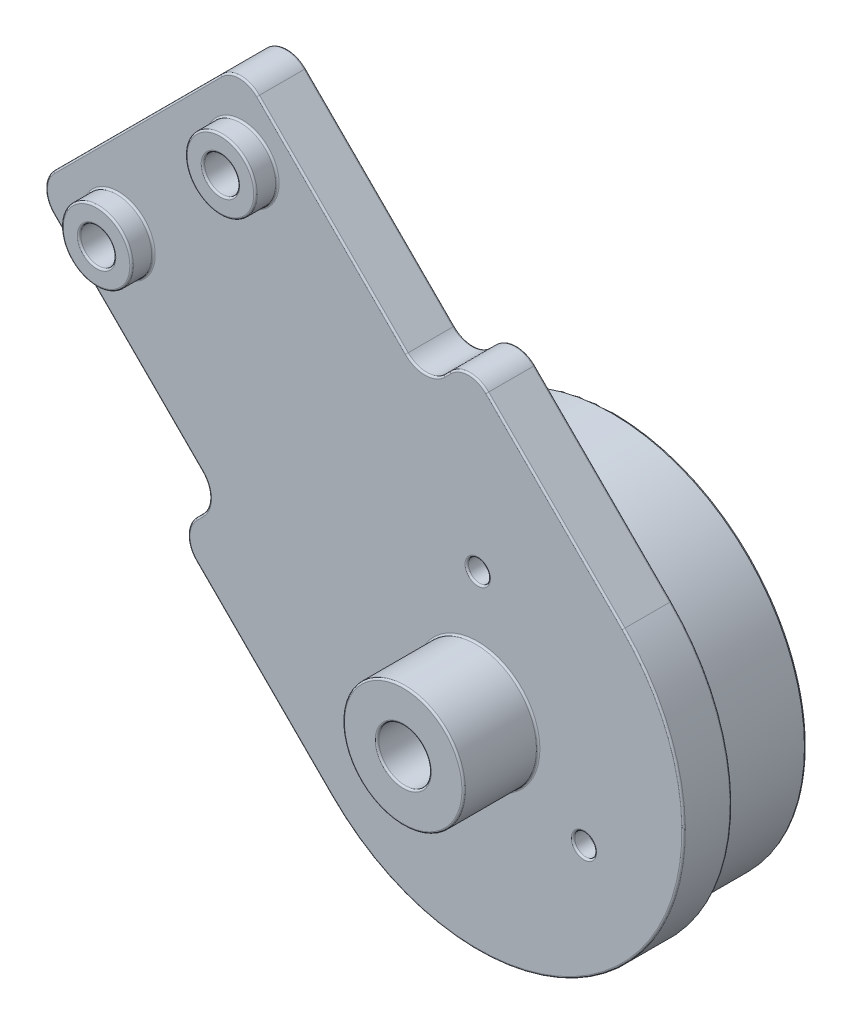
SolidWorks part; units mm, degrees
ref_plane "Front Plane" through (0, 0, 0) normal (0, 0, 1) x (1, 0, 0)
ref_plane "Top Plane" through (0, 0, 0) normal (0, 1, 0) x (1, 0, 0)
ref_plane "Right Plane" through (0, 0, 0) normal (1, 0, 0) x (0, 0, -1)
sketch "Sketch1" plane through (0, 0, 0) normal (0, 0, 1) x (1, 0, 0)
  line L0 (-100, 0) -> (100, 0) construction
  line L1 (-100, 0) -> (0, 100) construction
  line L2 (0, 100) -> (100, 0) construction
  line L3 (0, 0) -> (-50, 50) construction
  line L4 (-40, 60) -> (40, 60) construction
  line L5 (0, 100) -> (0, 60) construction
  circle A0 centre (-100, 0) radius 20
  circle A1 centre (0, 0) radius 20
  circle A2 centre (100, 0) radius 20
  point P2 (0, 0)
  dimension "D5" = 40
  dimension "D1" = 200
  dimension "D2" = 90
  dimension "D3" = 90
  dimension "D4" = 80
sketch "Sketch2" plane through (0, 0, 0) normal (0, 0, 1) x (1, 0, 0)
  line L0 (93.636, 20.5061) -> (79.4939, 6.364)
  line L1 (90.9809, 17.8509) -> (104.534, 4.6576)
  line L2 (-57.0711, 42.9289) -> (-40, 60) construction
  line L3 (-100, 0) -> (0, 100) construction
  line L4 (-40, 60) -> (40, 60) construction
  line L5 (40, 60) -> (86.565, 13.435) construction
  line L6 (0, 100) -> (100, 0) construction
  line L7 (-50, 35.8579) -> (-35.8579, 50)
  line L8 (-35.8579, 50) -> (35.8579, 50)
  line L9 (35.8579, 50) -> (79.4939, 6.364)
  line L10 (-64.1421, 50) -> (-44.1421, 70)
  line L11 (-44.1421, 70) -> (44.1421, 70)
  line L12 (44.1421, 70) -> (93.636, 20.5061)
  line L13 (-64.1421, 50) -> (-50, 35.8579)
  line L14 (82.1491, 9.0191) -> (95.3424, -4.534)
  line L15 (90.1005, 24.0416) -> (75.9584, 9.8995) construction
  line L17 (0, 100) -> (0, 60) construction
  line L18 (6, 70) -> (3.4304, 82.6944)
  line L19 (-6, 70) -> (-3.4304, 82.6944)
  circle A0 centre (100, 0) radius 3.5
  circle A1 centre (100, 0) radius 10 construction
  arc A2 (95.3424, -4.534) -> (104.534, 4.6576) centre (100, 0) ccw
  circle A3 centre (100, 0) radius 20 construction
  circle A4 centre (100, 0) radius 6.5 construction
  circle A5 centre (86.565, 20.5061) radius 1
  circle A6 centre (79.4939, 13.435) radius 1
  circle A7 centre (0, 60) radius 1.5
  circle A9 centre (0, 82) radius 1.5
  arc A10 (3.4304, 82.6944) -> (-3.4304, 82.6944) centre (0, 82) ccw
  circle A11 centre (0, 82) radius 3.5 construction
  circle A13 centre (-50, 50) radius 1.5
  dimension "D4" = 20
  dimension "D5" = 7
  dimension "D9" = 2
  dimension "D12" = 3
  dimension "D18" = 3
  dimension "D3" = 20
  dimension "D7" = 19
  dimension "D8" = 5
  dimension "D10" = 5
  dimension "D11" = 5
  dimension "D13" = 12
  dimension "D15" = 6
  dimension "D16" = 6
  dimension "D1" = 10
  dimension "D2" = 10
  dimension "D6" = 3
  dimension "D14" = 2
sketch "Sketch3" plane through (0, 0, 0) normal (0, 0, 1) x (1, 0, 0)
  line L0 (-86.565, 13.435) -> (-50, 50) construction
  line L1 (-100, 0) -> (0, 100) construction
  line L2 (-50, 50) -> (-13.435, 13.435) construction
  line L3 (0, 0) -> (-50, 50) construction
  line L4 (-79.4939, 6.364) -> (-50, 35.8579)
  line L5 (-50, 35.8579) -> (-20.5061, 6.364)
  line L6 (-93.636, 20.5061) -> (-50, 64.1421)
  line L7 (-50, 64.1421) -> (-6.364, 20.5061)
  line L8 (-79.4939, 6.364) -> (-50, 35.8579) construction
  line L9 (-93.636, 20.5061) -> (-50, 64.1421) construction
  line L10 (-93.636, 20.5061) -> (-79.4939, 6.364)
  line L11 (-6.364, 20.5061) -> (-20.5061, 6.364)
  line L12 (-104.534, 4.6576) -> (-90.9809, 17.8509)
  line L13 (-95.4038, -4.5962) -> (-81.9688, 8.8388)
  line L14 (4.5962, 4.5962) -> (-8.8388, 18.0312)
  line L15 (-4.5962, -4.5962) -> (-18.0312, 8.8388)
  line L16 (-90.1005, 24.0416) -> (-75.9584, 9.8995) construction
  line L17 (-9.8995, 24.0416) -> (-24.0416, 9.8995) construction
  circle A0 centre (-100, 0) radius 3.5
  circle A1 centre (0, 0) radius 3.5
  circle A2 centre (-100, 0) radius 10 construction
  circle A3 centre (0, 0) radius 10 construction
  arc A4 (-104.534, 4.6576) -> (-95.4038, -4.5962) centre (-100, 0) ccw
  arc A5 (-4.5962, -4.5962) -> (4.5962, 4.5962) centre (0, 0) ccw
  circle A6 centre (-100, 0) radius 20 construction
  circle A7 centre (-100, 0) radius 6.5 construction
  circle A8 centre (0, 0) radius 6.5 construction
  circle A9 centre (-86.565, 20.5061) radius 1
  circle A10 centre (-79.4939, 13.435) radius 1
  circle A11 centre (-20.5061, 13.435) radius 1
  circle A12 centre (-13.435, 20.5061) radius 1
  circle A13 centre (-50, 50) radius 1.5 construction
  circle A14 centre (-50, 50) radius 1.5
  dimension "D1" = 7
  dimension "D2" = 20
  dimension "D3" = 3
  dimension "D8" = 2
  dimension "D6" = 19
  dimension "D7" = 19
  dimension "D9" = 5
  dimension "D10" = 5
  dimension "D11" = 5
  dimension "D12" = 5
  dimension "D13" = 5
  dimension "D14" = 5
  dimension "D4" = 10
  dimension "D5" = 10
sketch "Sketch5" plane through (0, 0, 0) normal (0, 0, 1) x (1, 0, 0)
  line L6 (4, 60) -> (4, 70)
  line L7 (-4, 60) -> (-4, 70)
  line L10 (-57.5, 93.3579) -> (57.5, 93.3579)
  line L11 (57.5, 93.3579) -> (57.5, 83.3579)
  line L12 (57.5, 83.3579) -> (44.1421, 70)
  line L13 (44.1421, 70) -> (-44.1421, 70)
  line L14 (-44.1421, 70) -> (-57.5, 83.3579)
  line L15 (-57.5, 83.3579) -> (-57.5, 93.3579)
  line L16 (-22.5, 84.8579) -> (22.5, 84.8579) construction
  line L17 (-22.5, 89.3579) -> (22.5, 89.3579)
  line L18 (-22.5, 80.3579) -> (22.5, 80.3579)
  circle A0 centre (0, 60) radius 1.5 construction
  circle A1 centre (0, 60) radius 1.5
  arc A2 (-4, 60) -> (4, 60) centre (0, 60) ccw
  circle A3 centre (0, 60) radius 4 construction
  arc A4 (-22.5, 89.3579) -> (-22.5, 80.3579) centre (-22.5, 84.8579) ccw
  arc A5 (22.5, 80.3579) -> (22.5, 89.3579) centre (22.5, 84.8579) ccw
  point P2 (0, 93.3579)
  point P7 (0, 84.8579)
  dimension "D1" = 115
  dimension "D2" = 10
  dimension "D3" = 2.5
  dimension "D4" = 45
  dimension "D5" = 9
  dimension "D6" = 4
sketch "Sketch6" plane through (0, 0, 0) normal (0, 0, 1) x (1, 0, 0)
  line L0 (86.3882, 25.2791) -> (74.7209, 13.6118)
  line L1 (0, 100) -> (100, 0) construction
  line L2 (90.1005, 24.0416) -> (75.9584, 9.8995) construction
  line L3 (74.7209, 13.6118) -> (85.3275, 3.0052)
  line L4 (85.3275, 3.0052) -> (82.8527, 0.5303)
  line L5 (82.8527, 0.5303) -> (91.6915, -8.3085)
  line L6 (100, 0) -> (88.4373, 11.5627) construction
  line L7 (99.4697, 17.1473) -> (108.3085, 8.3085)
  line L8 (96.9948, 14.6725) -> (99.4697, 17.1473)
  line L9 (86.3882, 25.2791) -> (96.9948, 14.6725)
  circle A0 centre (100, 0) radius 10 construction
  circle A1 centre (100, 0) radius 10
  arc A2 (91.6915, -8.3085) -> (108.3085, 8.3085) centre (100, 0) ccw
  circle A3 centre (100, 0) radius 11.75 construction
  circle A4 centre (86.565, 20.5061) radius 1 construction
  circle A5 centre (79.4939, 13.435) radius 1 construction
  circle A6 centre (86.565, 20.5061) radius 1
  circle A7 centre (79.4939, 13.435) radius 1
  point P9 (80.5546, 19.4454)
  dimension "D2" = 16.5
  dimension "D3" = 12.5
  dimension "D4" = 15
  dimension "D1" = 1.75
extrude "Boss-Extrude1" add sketch "Sketch6" along normal blind 2.75
sketch "Sketch7" plane through (0, 0, 2.75) normal (0, 0, 1) x (1, 0, 0)
  circle A0 centre (100, 0) radius 10 construction
  circle A1 centre (100, 0) radius 10
extrude "Boss-Extrude2" add sketch "Sketch7" against normal blind 1
sketch "Sketch9" plane through (0, 0, 0) normal (0, 0, -1) x (-1, 0, 0)
  circle A0 centre (-100, 0) radius 11
  circle A1 centre (-100, 0) radius 10
  circle A2 centre (-100, 0) radius 10
  dimension "D1" = 0
  dimension "D2" = 1
extrude "Boss-Extrude3" add sketch "Sketch9" along normal blind 5
fillet "Fillet1" radius 1.5 6 edges at (96.9948, 14.6725, 1.375) (99.4697, 17.1473, 1.375) (82.8527, 0.5303, 1.375) (85.3275, 3.0052, 1.375) (74.7209, 13.6118, 1.375) (86.3882, 25.2791, 1.375)
sketch "Sketch10" plane through (0, 0, 2.75) normal (0, 0, 1) x (1, 0, 0)
  circle A0 centre (79.4939, 13.435) radius 1 construction
  circle A1 centre (86.565, 20.5061) radius 1 construction
  circle A2 centre (79.4939, 13.435) radius 1
  circle A3 centre (86.565, 20.5061) radius 1
  circle A4 centre (79.4939, 13.435) radius 2
  circle A5 centre (86.565, 20.5061) radius 2
  dimension "D1" = 1
extrude "Boss-Extrude4" add sketch "Sketch10" along normal blind 1.25
sketch "Sketch11" plane through (0, 0, 2.75) normal (0, 0, 1) x (1, 0, 0)
  circle A0 centre (100, 0) radius 1.5
  dimension "D1" = 3
extrude "Cut-Extrude1" cut sketch "Sketch11" against normal up to surface (1 mm away) up to face at (110, 0, 1.75)
sketch "Sketch12" plane through (0, 0, 2.75) normal (0, 0, 1) x (1, 0, 0)
  circle A0 centre (100, 0) radius 1.5 construction
  circle A1 centre (100, 0) radius 1.5
  circle A2 centre (100, 0) radius 3.45
  dimension "D1" = 6.9
extrude "Boss-Extrude5" add sketch "Sketch12" along normal blind 4.25
sketch "Sketch13" plane through (0, 0, 2.75) normal (0, 0, 1) x (1, 0, 0)
  line L0 (100, 0) -> (100, 7) construction
  circle A0 centre (100, 7) radius 0.625
  circle A1 centre (106.0622, -3.5) radius 0.625
  circle A2 centre (93.9378, -3.5) radius 0.625
  point P11 (100, 0)
  dimension "D1" = 1.25
  dimension "D2" = 7
  dimension "D3" = 3
extrude "Cut-Extrude2" cut sketch "Sketch13" against normal up to surface (1 mm away) up to face at (101.5, 0, 1.75)
fillet "Fillet2" radius 0.1 50 edges at (94.5628, -3.5, 1.75) (94.5628, -3.5, 2.75) (106.6872, -3.5, 1.75) (106.6872, -3.5, 2.75) (100.625, 7, 2.75) (100.625, 7, 1.75) (101.5, 0, 7) (103.45, 0, 2.75) (103.45, 0, 7) (101.5, 0, 1.75) (88.565, 20.5061, 4) (88.565, 20.5061, 2.75) (87.565, 20.5061, 4) (80.4939, 13.435, 4) (81.4939, 13.435, 2.75) (81.4939, 13.435, 4) (90, 0, -5) (89, 0, -5) (110, 0, 1.75) (80.4939, 13.435, 0) (87.565, 20.5061, 0) (91.6915, 19.9758, 0) (80.5546, 19.4454, 0) (80.0242, 8.3085, 0) (84.0901, 1.7678, 0) (87.8024, -4.4194, 0) (108.3085, -8.3085, 0) (104.4194, 12.1976, 0) (98.2322, 15.9099, 0) (91.6915, 19.9758, 2.75) (80.5546, 19.4454, 2.75) (84.0901, 1.7678, 2.75) (87.8024, -4.4194, 2.75) (108.3085, -8.3085, 2.75) (104.4194, 12.1976, 2.75) (98.2322, 15.9099, 2.75) (111, 0, 0) (86.3882, 24.6577, 0) (75.3423, 13.6118, 0) (83.474, 0.5303, 0) (99.4697, 16.526, 0) (86.3882, 24.6577, 2.75) (75.3423, 13.6118, 2.75) (83.474, 0.5303, 2.75) (99.4697, 16.526, 2.75) (96.9948, 15.2938, 0) (96.9948, 15.2938, 2.75) (84.7062, 3.0052, 0) (84.7062, 3.0052, 2.75) (80.0242, 8.3085, 2.75)
